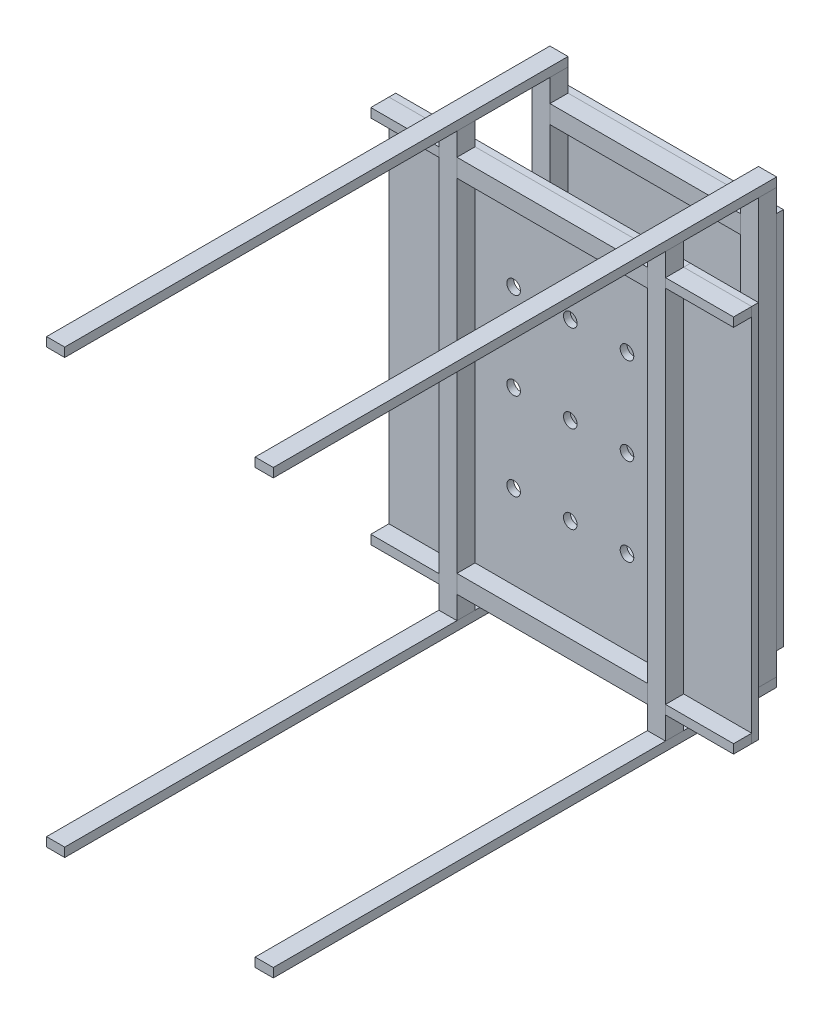
SolidWorks part; units mm, degrees
ref_plane "Front Plane" through (0, 0, 0) normal (0, 0, 1) x (1, 0, 0)
ref_plane "Top Plane" through (0, 0, 0) normal (0, 1, 0) x (1, 0, 0)
ref_plane "Right Plane" through (0, 0, 0) normal (1, 0, 0) x (0, 0, -1)
sketch "Sketch1" plane through (0, 0, 0) normal (0, 0, 1) x (1, 0, 0)
  line L1 (0, 0) -> (-1000, 0)
  line L2 (0, 0) -> (0, -1950)
  line L3 (0, -1950) -> (-1000, -1950)
  line L4 (-1000, 0) -> (-1000, -1950)
  dimension "D1" = 1000
  dimension "D2" = 1950
extrude "Boss-Extrude1" add sketch "Sketch1" along normal blind 30
sketch "Sketch2" plane through (0, 0, 30) normal (0, 0, 1) x (1, 0, 0)
  line L0 (-80, 0) -> (0, 0)
  line L1 (-1000, 0) -> (-920, 0)
  line L2 (-1000, 0) -> (-1000, -40)
  line L3 (-1000, -40) -> (-920, -40)
  line L4 (-920, 0) -> (-920, -40)
  line L5 (-80, 0) -> (-80, -40)
  line L6 (-80, -40) -> (0, -40)
  line L7 (0, 0) -> (0, -40)
  line L8 (-80, -1910) -> (0, -1910)
  line L9 (-80, -1910) -> (-80, -1950)
  line L10 (-80, -1950) -> (0, -1950)
  line L11 (0, -1910) -> (0, -1950)
  line L12 (-1000, -1910) -> (-920, -1910)
  line L13 (-1000, -1910) -> (-1000, -1950)
  line L14 (-1000, -1950) -> (-920, -1950)
  line L15 (-920, -1910) -> (-920, -1950)
  dimension "D1" = 80
  dimension "D2" = 40
  dimension "D3" = 80
  dimension "D4" = 40
  dimension "D5" = 80
  dimension "D6" = 40
  dimension "D7" = 80
  dimension "D8" = 40
extrude "Boss-Extrude2" add sketch "Sketch2" along normal blind 2220 separate body
sketch "Sketch3" plane through (0, -1910, 0) normal (0, 1, 0) x (1, 0, 0)
  line L0 (0, -2250) -> (0, -30) construction
  line L1 (-80, -30) -> (0, -30)
  line L2 (-80, -30) -> (-80, -110)
  line L3 (-80, -110) -> (0, -110)
  line L4 (0, -30) -> (0, -110)
  line L5 (-920, -2250) -> (-920, -30) construction
  line L6 (-1000, -30) -> (-920, -30)
  line L7 (-1000, -30) -> (-1000, -110)
  line L8 (-1000, -110) -> (-920, -110)
  line L9 (-920, -30) -> (-920, -110)
  dimension "D1" = 80
extrude "Boss-Extrude3" add sketch "Sketch3" along normal up to surface (1870 mm away) separate body up to face at (-960, -40, 1140)
sketch "Sketch4" plane through (-920, 0, 0) normal (1, 0, 0) x (0, 0, -1)
  line L0 (-110, -40) -> (-110, -1910) construction
  line L1 (-30, -113.0488) -> (-110, -113.0488)
  line L2 (-30, -113.0488) -> (-30, -73.0488)
  line L3 (-30, -73.0488) -> (-110, -73.0488)
  line L4 (-110, -113.0488) -> (-110, -73.0488)
  line L5 (-110, -1910) -> (-30, -1910)
  line L6 (-110, -1910) -> (-110, -1950)
  line L7 (-110, -1950) -> (-30, -1950)
  line L8 (-30, -1910) -> (-30, -1950)
  line L9 (-30, -40) -> (-30, -1910) construction
  dimension "D1" = 40
extrude "Boss-Extrude4" [suppressed] add sketch "Sketch4" along normal up to surface (840 mm away) separate body
sketch "Sketch5" plane through (0, -1910, 0) normal (0, 1, 0) x (1, 0, 0)
  line L0 (-1000, -2250) -> (-1000, -30) construction
  line L1 (-1000, -440) -> (-920, -440)
  line L2 (-1000, -440) -> (-1000, -520)
  line L3 (-1000, -520) -> (-920, -520)
  line L4 (-920, -440) -> (-920, -520)
  line L5 (-920, -2250) -> (-920, -30) construction
  line L6 (-1000, -110) -> (-920, -110) construction
  line L7 (-80, -2250) -> (-80, -30) construction
  line L8 (-80, -440) -> (0, -440)
  line L9 (-80, -440) -> (-80, -520)
  line L10 (-80, -520) -> (0, -520)
  line L11 (0, -440) -> (0, -520)
  line L12 (0, -2250) -> (0, -30) construction
  point P8 (-960, -110)
  dimension "D1" = 80
  dimension "D2" = 330
extrude "Boss-Extrude5" add sketch "Sketch5" along normal up to surface (1870 mm away) separate body up to face at (-40, -40, 1140)
sketch "Sketch6" plane through (0, 0, 440) normal (0, 0, -1) x (-1, 0, 0)
  line L1 (1000, -1810) -> (0, -1810)
  line L2 (1000, -1810) -> (1000, -140)
  line L3 (1000, -140) -> (0, -140)
  line L4 (0, -1810) -> (0, -140)
  line L5 (920, -1910) -> (1000, -1910) construction
  dimension "D1" = 100
  dimension "D2" = 100
extrude "Boss-Extrude6" add sketch "Sketch6" along normal blind 30 separate body
sketch "Sketch7" plane through (0, 0, 0) normal (1, 0, 0) x (0, 0, -1)
  line L1 (-440, -180) -> (-520, -180)
  line L2 (-440, -180) -> (-440, -140)
  line L3 (-440, -140) -> (-520, -140)
  line L4 (-520, -180) -> (-520, -140)
  line L6 (-520, -1770) -> (-440, -1770)
  line L7 (-520, -1770) -> (-520, -1810)
  line L8 (-520, -1810) -> (-440, -1810)
  line L9 (-440, -1770) -> (-440, -1810)
  line L13 (-520, -40) -> (-520, -1910) construction
  line L17 (-440, -40) -> (-440, -1910) construction
  line L18 (-520, -40) -> (-440, -40) construction
  line L19 (-520, -1910) -> (-440, -1910) construction
  dimension "D1" = 40
  dimension "D2" = 40
  dimension "D3" = 100
  dimension "D4" = 100
extrude "Boss-Extrude7" add sketch "Sketch7" along normal blind 300 separate body
sketch "Sketch8" plane through (0, 0, 440) normal (0, 0, -1) x (-1, 0, 0)
  line L0 (-300, -1810) -> (-300, -1770) construction
  line L1 (0, -140) -> (-300, -140)
  line L2 (0, -140) -> (0, -1810)
  line L3 (0, -1810) -> (-300, -1810)
  line L4 (-300, -140) -> (-300, -1810)
  line L5 (-300, -1810) -> (0, -1810) construction
extrude "Boss-Extrude9" add sketch "Sketch8" along normal blind 30 separate body
sketch "Sketch9" plane through (0, 0, 0) normal (0, 0, -1) x (-1, 0, 0)
  line L0 (0, -1950) -> (0, 0) construction
  line L1 (0, -140) -> (1000, -140)
  line L2 (0, -140) -> (0, 0)
  line L3 (0, 0) -> (1000, 0)
  line L4 (1000, -140) -> (1000, 0)
  line L5 (1000, -1950) -> (0, -1950)
  line L6 (1000, -1950) -> (1000, -1810)
  line L7 (1000, -1810) -> (0, -1810)
  line L8 (0, -1950) -> (0, -1810)
  line L9 (-300, -1810) -> (0, -1810) construction
extrude "Cut-Extrude1" cut sketch "Sketch9" against normal up to vertex (30 mm away) up to point (0, -1950, 30)
sketch "Sketch11" plane through (-920, 0, 0) normal (1, 0, 0) x (0, 0, -1)
  line L0 (-30, -40) -> (-30, -1910) construction
  line L1 (-30, -139.9926) -> (-110, -139.9926)
  line L2 (-30, -139.9926) -> (-30, -219.9926)
  line L3 (-30, -219.9926) -> (-110, -219.9926)
  line L4 (-110, -139.9926) -> (-110, -219.9926)
  line L5 (-440, -40) -> (-440, -1910) construction
  line L6 (-440, -139.9926) -> (-520, -139.9926)
  line L7 (-440, -139.9926) -> (-440, -219.9926)
  line L8 (-440, -219.9926) -> (-520, -219.9926)
  line L9 (-520, -139.9926) -> (-520, -219.9926)
  line L10 (-520, -40) -> (-520, -1910) construction
  line L11 (-110, -40) -> (-110, -1910) construction
  line L13 (-440, -1809.3907) -> (-520, -1809.3907)
  line L14 (-440, -1809.3907) -> (-440, -1729.3907)
  line L15 (-440, -1729.3907) -> (-520, -1729.3907)
  line L16 (-520, -1809.3907) -> (-520, -1729.3907)
  line L17 (-30, -1809.3907) -> (-110, -1809.3907)
  line L18 (-30, -1809.3907) -> (-30, -1729.3907)
  line L19 (-30, -1729.3907) -> (-110, -1729.3907)
  line L20 (-110, -1809.3907) -> (-110, -1729.3907)
  dimension "D1" = 80
  dimension "D2" = 80
extrude "Boss-Extrude10" add sketch "Sketch11" along normal up to surface (840 mm away) separate body up to face at (-80, -975, 480)
sketch "Sketch12" plane through (-1000, 0, 0) normal (-1, 0, 0) x (0, 0, 1)
  line L1 (410, -140) -> (440, -140)
  line L2 (410, -140) -> (410, -1810)
  line L3 (410, -1810) -> (440, -1810)
  line L4 (440, -140) -> (440, -1810)
extrude "Boss-Extrude11" add sketch "Sketch12" along normal blind 300 separate body
sketch "Sketch13" plane through (-1000, 0, 0) normal (-1, 0, 0) x (0, 0, 1)
  line L0 (520, -40) -> (520, -1910) construction
  line L1 (440, -140) -> (520, -140)
  line L2 (440, -140) -> (440, -180)
  line L3 (440, -180) -> (520, -180)
  line L4 (520, -140) -> (520, -180)
  line L6 (440, -1810) -> (520, -1810)
  line L7 (440, -1810) -> (440, -1770)
  line L8 (440, -1770) -> (520, -1770)
  line L9 (520, -1810) -> (520, -1770)
  dimension "D1" = 40
  dimension "D2" = 40
extrude "Boss-Extrude12" add sketch "Sketch13" along normal blind 300 separate body
sketch "Sketch14" plane through (0, 0, 440) normal (0, 0, 1) x (1, 0, 0)
  line L0 (-80, -139.9926) -> (-920, -139.9926) construction
  line L3 (-1000, -40) -> (-1000, -1910) construction
  line L5 (-80, -1809.3907) -> (-920, -1809.3907) construction
  line L6 (0, -1810) -> (0, -140) construction
  circle A0 centre (-750, -589.9926) radius 30
  circle A1 centre (-500, -589.9926) radius 30
  circle A2 centre (-250, -589.9926) radius 30
  circle A3 centre (-500, -974.6916) radius 30
  circle A4 centre (-250, -974.6916) radius 30
  circle A5 centre (-500, -1359.3907) radius 30
  circle A6 centre (-250, -1359.3907) radius 30
  circle A7 centre (-750, -974.6916) radius 30
  circle A8 centre (-750, -1359.3907) radius 30
  dimension "D1" = 60
  dimension "D6" = 450
  dimension "D2" = 450
  dimension "D3" = 250
  dimension "D4" = 3
  dimension "D7" = 250
  dimension "D5" = 3
extrude "Cut-Extrude2" cut sketch "Sketch14" against normal through all and the other way through all
equation "\"AA\"=40"
equation "\"D1@Sketch7\"=\"AA\""
equation "\"D1@Sketch5\"=\"AA\"*2"
equation "\"D3@Sketch2\"=2*\"AA\""
equation "\"D4@Sketch2\"=\"AA\""
equation "\"D2@Sketch2\"=\"AA\""
equation "\"D1@Sketch2\"=2*\"AA\""
equation "\"D7@Sketch2\"=2*\"AA\""
equation "\"D8@Sketch2\"=\"AA\""
equation "\"D6@Sketch2\"=\"AA\""
equation "\"D5@Sketch2\"=2*\"AA\""
equation "\"D1@Sketch4\"=\"AA\""
equation "\"D1@Sketch3\"=\"AA\"*2"
equation "\"D1@Sketch11\"=\"AA\"*2"
equation "\"D2@Sketch11\"=\"AA\"*2"
equation "\"D1@Sketch13\"=\"AA\""
equation "\"D2@Sketch13\"=\"AA\""
equation "\"D2@Sketch7\"=\"AA\""
